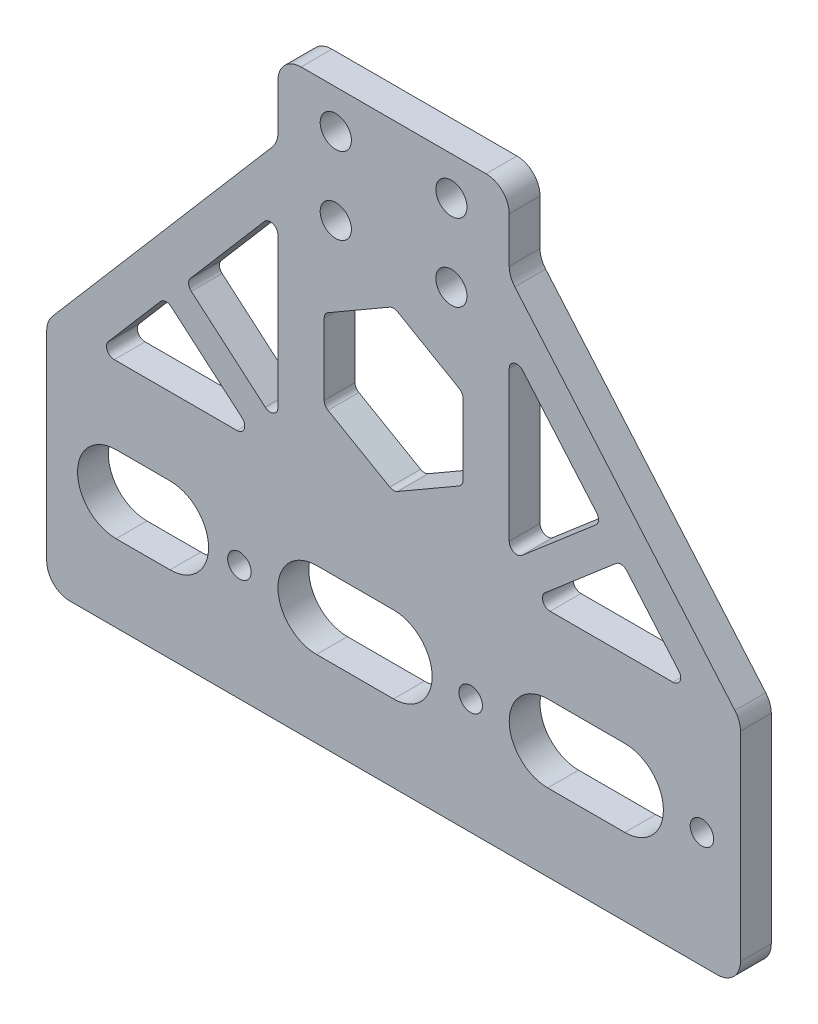
SolidWorks part; units mm, degrees
material "Thornel Mat VMA"
ref_plane "前视基准面" through (0, 0, 0) normal (0, 0, 1) x (1, 0, 0)
ref_plane "上视基准面" through (0, 0, 0) normal (0, 1, 0) x (1, 0, 0)
ref_plane "右视基准面" through (0, 0, 0) normal (1, 0, 0) x (0, 0, -1)
other "Configuration Table"
sketch "草图1" plane through (0, 0, 0) normal (0, 0, 1) x (1, 0, 0)
  line L0 (-45, 0) -> (45, 0)
  line L1 (45, 0) -> (45, 30)
  line L2 (45, 30) -> (15, 30)
  line L3 (15, 30) -> (15, 65)
  line L4 (15, 65) -> (-15, 65)
  line L5 (-15, 65) -> (-15, 30)
  line L6 (-15, 30) -> (-45, 30)
  line L7 (-45, 30) -> (-45, 0)
  line L8 (0, 65) -> (0, 0) construction
  dimension "D1" = 30
  dimension "D2" = 30
  dimension "D3" = 30
  dimension "D4" = 35
extrude "凸台-拉伸1" add sketch "草图1" along normal blind 4
sketch "草图4" plane through (0, 0, 4) normal (0, 0, 1) x (1, 0, 0)
  line L0 (-45, 30) -> (-15, 65)
  line L1 (15, 65) -> (45, 30)
  line L2 (45, 30) -> (15, 30) construction
  line L3 (15, 30) -> (15, 65) construction
  line L4 (-15, 30) -> (-45, 30) construction
  line L5 (-15, 65) -> (-15, 30) construction
  line L6 (45, 30) -> (15, 30)
  line L7 (15, 30) -> (15, 65)
  line L8 (-15, 30) -> (-45, 30)
  line L9 (-15, 65) -> (-15, 30)
extrude "凸台-拉伸2" add sketch "草图4" against normal up to surface (4 mm away) up to face at (0, 31.25, 0)
sketch "草图5" plane through (0, 0, 4) normal (0, 0, 1) x (1, 0, 0)
  line L0 (-38.4146, 30) -> (-15, 30)
  line L1 (-15, 30) -> (-15, 57.317)
  line L2 (-15, 57.317) -> (-38.4146, 30)
  line L3 (-15, 65) -> (-45, 30) construction
  line L4 (0, 65) -> (0, 0) construction
  line L5 (15, 65) -> (-15, 65) construction
  line L6 (15, 57.317) -> (38.4146, 30)
  line L7 (15, 30) -> (15, 57.317)
  line L8 (38.4146, 30) -> (15, 30)
  dimension "D1" = 5
extrude "切除-拉伸2" cut sketch "草图5" against normal up to surface (4 mm away) up to face at (0, 31.6667, 0)
sketch "草图6" plane through (0, 0, 4) normal (0, 0, 1) x (1, 0, 0)
  line L1 (0, 54.0508) -> (-9, 48.8547)
  line L2 (-9, 48.8547) -> (-9, 38.4624)
  line L3 (-9, 38.4624) -> (0, 33.2662)
  line L4 (0, 33.2662) -> (9, 38.4624)
  line L5 (9, 38.4624) -> (9, 48.8547)
  line L6 (9, 48.8547) -> (0, 54.0508)
  line L7 (15, 57.317) -> (15, 30) construction
  circle A0 centre (0, 43.6585) radius 9 construction
  point P11 (15, 43.6585)
  dimension "D1" = 18
extrude "切除-拉伸3" cut sketch "草图6" against normal up to surface (4 mm away) up to face at (-22.8049, 39.1057, 0)
sketch "草图8" plane through (0, 0, 0) normal (0, 0, -1) x (-1, 0, 0)
  circle A0 centre (20, 15) radius 1.525
  circle A1 centre (-10, 15) radius 1.525
  circle A2 centre (-40, 15) radius 1.525
  dimension "D1" = 3.05
extrude "切除-拉伸4" cut sketch "草图8" against normal blind 10
sketch "草图9" plane through (0, 0, 0) normal (0, 0, -1) x (-1, 0, 0)
  line L0 (0, 0) -> (0, 65) construction
  line L1 (-15, 65) -> (15, 65) construction
  circle A0 centre (-7.5, 60) radius 2.025
  circle A1 centre (7.5, 60) radius 2.025
  dimension "D1" = 4.05
  dimension "D2" = 15
  dimension "D3" = 5
extrude "切除-拉伸5" cut sketch "草图9" against normal blind 10
sketch "草图10" plane through (0, 0, 4) normal (0, 0, 1) x (1, 0, 0)
  line L0 (-10, 15) -> (0, 15) construction
  line L1 (-10, 20) -> (0, 20)
  line L2 (-10, 10) -> (0, 10)
  line L3 (-20, 15) -> (10, 15) construction
  line L4 (10, 15) -> (40, 15) construction
  line L5 (20, 15) -> (30, 15) construction
  line L6 (20, 20) -> (30, 20)
  line L7 (20, 10) -> (30, 10)
  line L8 (-20, 15) -> (-45, 15) construction
  line L9 (-45, 30) -> (-45, 0) construction
  line L10 (-36, 15) -> (-29, 15) construction
  line L11 (-36, 20) -> (-29, 20)
  line L12 (-36, 10) -> (-29, 10)
  arc A0 (-10, 20) -> (-10, 10) centre (-10, 15) ccw
  arc A1 (0, 10) -> (0, 20) centre (0, 15) ccw
  arc A2 (20, 20) -> (20, 10) centre (20, 15) ccw
  arc A3 (30, 10) -> (30, 20) centre (30, 15) ccw
  arc A4 (-36, 20) -> (-36, 10) centre (-36, 15) ccw
  arc A5 (-29, 10) -> (-29, 20) centre (-29, 15) ccw
  point P2 (-5, 15)
  point P10 (25, 15)
  point P25 (-32.5, 15)
  dimension "D1" = 5
  dimension "D4" = 5
  dimension "D2" = 10
  dimension "D3" = 7
extrude "切除-拉伸6" cut sketch "草图10" against normal through all both
sketch "草图11" plane through (0, 0, 4) normal (0, 0, 1) x (1, 0, 0)
  line L0 (-15, 65) -> (-15, 75)
  line L1 (-15, 75) -> (15, 75)
  line L2 (15, 75) -> (15, 65)
  line L3 (-15, 65) -> (15, 65)
  line L4 (7.5, 60) -> (7.5, 70) construction
  line L5 (-7.5, 70) -> (-7.5, 60) construction
  circle A0 centre (7.5, 70) radius 2.025
  circle A1 centre (-7.5, 70) radius 2.025
  dimension "D2" = 4.05
  dimension "D3" = 5
  dimension "D1" = 5
extrude "凸台-拉伸3" add sketch "草图11" against normal up to surface (4 mm away) up to face at (-32.5, 15, 0)
fillet "圆角2" radius 3 8 edges at (-45, 30, 2) (-45, 0, 2) (45, 0, 2) (45, 30, 2) (15, 65, 2) (15, 75, 2) (-15, 65, 2) (-15, 75, 2)
sketch "草图13" plane through (0, 0, 4) normal (0, 0, 1) x (1, 0, 0)
  line L0 (15, 33.037) -> (26.9972, 43.3203)
  line L1 (15, 57.317) -> (15, 30) construction
  line L2 (38.4146, 30) -> (15, 57.317) construction
  line L3 (29.6004, 40.2833) -> (17.6032, 30)
  line L4 (15, 30) -> (38.4146, 30) construction
  line L5 (26.9972, 43.3203) -> (29.6004, 40.2833)
  line L6 (15, 33.037) -> (15, 30)
  line L7 (15, 30) -> (17.6032, 30)
  dimension "D1" = 4
extrude "凸台-拉伸4" add sketch "草图13" against normal up to surface (4 mm away) up to face at (-32.5, 15, 0)
mirror "镜向1" about plane through (0, 0, 0) normal (1, 0, 0) of "凸台-拉伸4"
fillet "圆角3" radius 1 18 edges at (9, 38.4624, 2) (0, 33.2662, 2) (-9, 38.4624, 2) (-9, 48.8547, 2) (0, 54.0508, 2) (9, 48.8547, 2) (38.4146, 30, 2) (17.6032, 30, 2) (29.6004, 40.2833, 2) (15, 57.317, 2) (26.9972, 43.3203, 2) (15, 33.037, 2) (-26.9972, 43.3203, 2) (-15, 57.317, 2) (-15, 33.037, 2) (-17.6032, 30, 2) (-29.6004, 40.2833, 2) (-38.4146, 30, 2)
